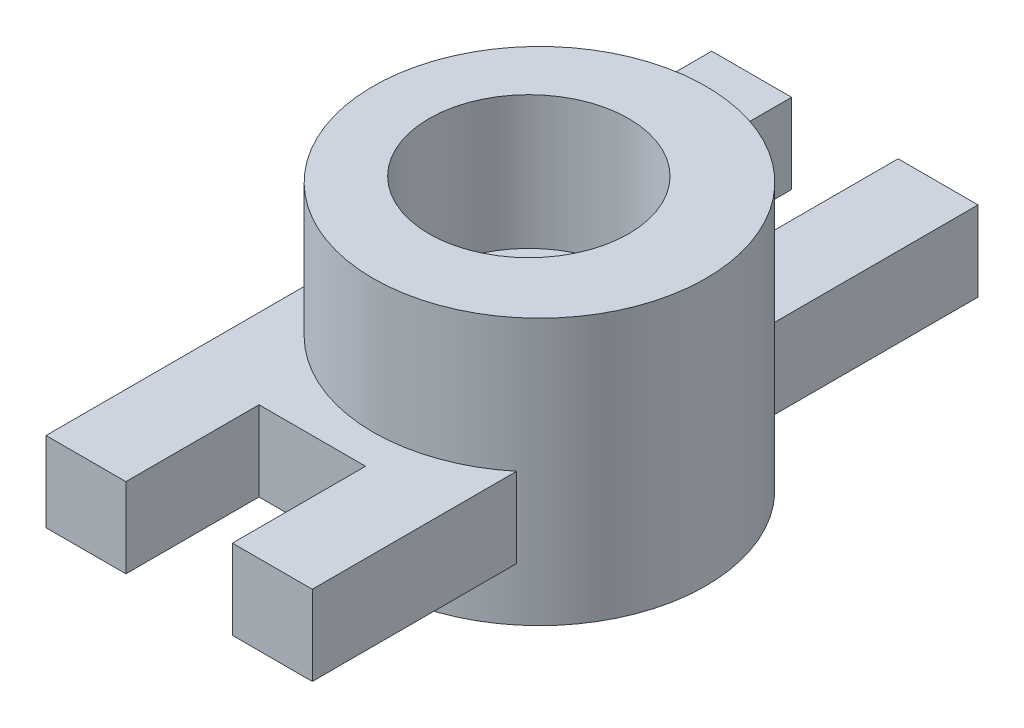
SolidWorks part; units mm, degrees
ref_plane "Front Plane" through (0, 0, 0) normal (0, 0, 1) x (1, 0, 0)
ref_plane "Top Plane" through (0, 0, 0) normal (0, 1, 0) x (1, 0, 0)
ref_plane "Right Plane" through (0, 0, 0) normal (1, 0, 0) x (0, 0, -1)
sketch "Sketch1" plane through (0, 0, 0) normal (1, 0, 0) x (0, 0, -1)
  line L1 (-34.9091, 5.8182) -> (65.0909, 5.8182)
  line L2 (-34.9091, 5.8182) -> (-34.9091, -6.1818)
  line L3 (-34.9091, -6.1818) -> (65.0909, -6.1818)
  line L4 (65.0909, 5.8182) -> (65.0909, -6.1818)
  dimension "D1" = 12
  dimension "D2" = 100
extrude "Boss-Extrude1" add sketch "Sketch1" against normal blind 40
sketch "Sketch3" plane through (0, 5.8182, 0) normal (0, 1, 0) x (1, 0, 0)
  line L0 (-40, 53.2615) -> (-30, 53.2615) construction
  line L2 (-40, 65.0909) -> (-40, -34.9091) construction
  line L3 (-20, -34.9091) -> (-20, 15.0909) construction
  line L4 (-40, -34.9091) -> (0, -34.9091) construction
  circle A0 centre (-17.4706, 15.0909) radius 15
  circle A2 centre (-15.8706, 15.0909) radius 25
  point P9 (-5.2836, 15.0909)
  point P10 (-99.5604, 16.9305)
  point P11 (-13.3316, 15.0909)
  point P16 (-17.4706, 15.0909)
  point P17 (-15.861, 15.0909)
  dimension "D2" = 30
  dimension "D3" = 50
  dimension "D4" = 50
  dimension "D5" = 1.6
  dimension "D1" = 10
extrude "Boss-Extrude3" add sketch "Sketch3" along normal mid plane 40
ref_plane "Plane8" through (0, 0, 34.9091) normal (0, 0, 1) x (1, 0, 0)
sketch "Sketch8" plane through (0, 0, 34.9091) normal (0, 0, 1) x (1, 0, 0)
  line L0 (-40, -6.1818) -> (-28, -6.1818) construction
  line L1 (-40, -6.1818) -> (0, -6.1818) construction
  line L2 (0, 5.8182) -> (-12, 5.8182) construction
  line L3 (0, 5.8182) -> (-40, 5.8182) construction
  line L4 (-40, 5.8182) -> (0, 5.8182) construction
  line L5 (-28, 5.8182) -> (-12, 5.8182)
  line L6 (-28, 5.8182) -> (-28, -6.1818)
  line L7 (-28, -6.1818) -> (-12, -6.1818)
  line L8 (-12, 5.8182) -> (-12, -6.1818)
  dimension "D1" = 12
  dimension "D2" = 12
extrude "Cut-Extrude3" cut sketch "Sketch8" against normal blind 20
ref_plane "Plane9" through (0, 0, -65.0909) normal (0, 0, -1) x (-1, 0, 0)
sketch "Sketch9" plane through (0, 0, -65.0909) normal (0, 0, -1) x (-1, 0, 0)
  line L0 (0, -6.1818) -> (12, -6.1818) construction
  line L1 (40, 5.8182) -> (28, 5.8182) construction
  line L2 (40, 5.8182) -> (0, 5.8182) construction
  line L3 (40, 5.8182) -> (0, 5.8182) construction
  line L4 (12, 5.8182) -> (28, 5.8182)
  line L5 (12, 5.8182) -> (12, -6.1818)
  line L6 (12, -6.1818) -> (28, -6.1818)
  line L7 (28, 5.8182) -> (28, -6.1818)
  line L8 (40, -6.1818) -> (0, -6.1818) construction
  dimension "D1" = 12
  dimension "D2" = 12
extrude "Cut-Extrude4" cut sketch "Sketch9" against normal blind 20
